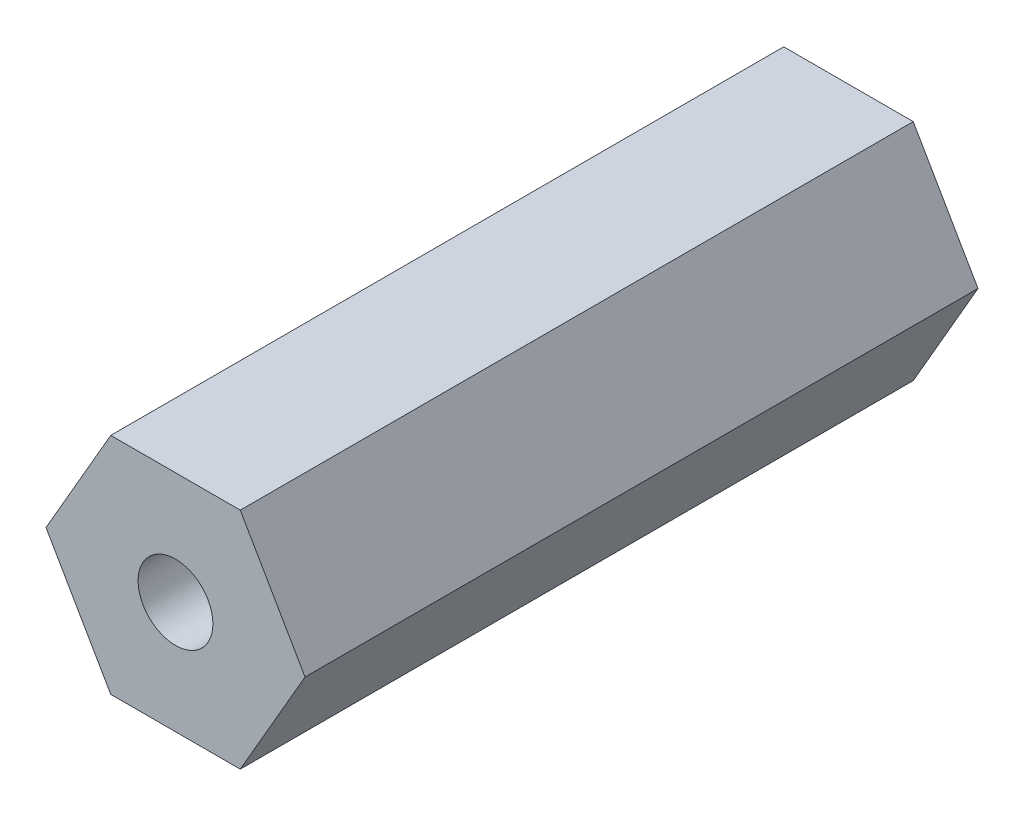
SolidWorks part; units mm, degrees
ref_plane "Front" through (0, 0, 0) normal (0, 0, 1) x (1, 0, 0)
ref_plane "Top" through (0, 0, 0) normal (0, 1, 0) x (1, 0, 0)
ref_plane "Right" through (0, 0, 0) normal (1, 0, 0) x (0, 0, -1)
sketch "Sketch1" plane through (0, 0, 0) normal (0, 0, 1) x (1, 0, 0)
  line L1 (3.4641, 0) -> (1.7321, 3)
  line L2 (1.7321, 3) -> (-1.7321, 3)
  line L3 (-1.7321, 3) -> (-3.4641, 0)
  line L4 (-3.4641, 0) -> (-1.7321, -3)
  line L5 (-1.7321, -3) -> (1.7321, -3)
  line L6 (1.7321, -3) -> (3.4641, 0)
  circle A0 centre (0, 0) radius 3 construction
  circle A1 centre (0, 0) radius 1
  dimension "D1" = 6
extrude "Boss-Extrude1" add sketch "Sketch1" along normal blind 18
